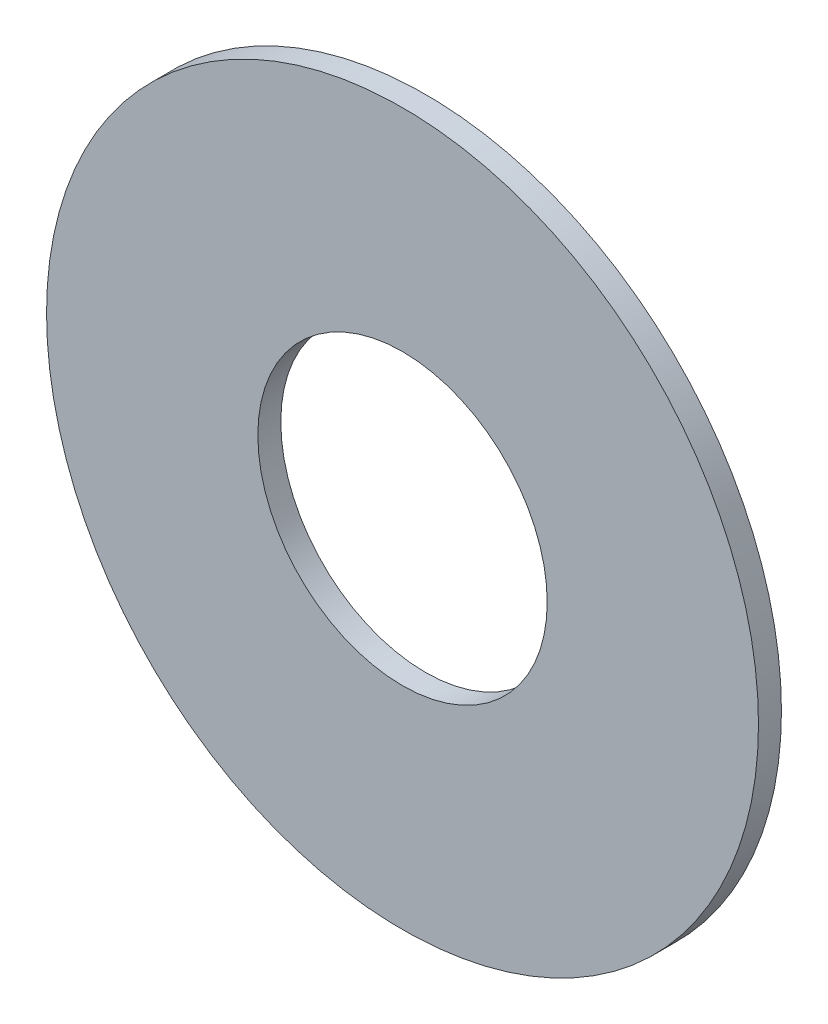
SolidWorks part; units mm, degrees
ref_plane "Front Plane" through (0, 0, 0) normal (0, 0, 1) x (1, 0, 0)
ref_plane "Top Plane" through (0, 0, 0) normal (0, 1, 0) x (1, 0, 0)
ref_plane "Right Plane" through (0, 0, 0) normal (1, 0, 0) x (0, 0, -1)
sketch "Sketch1" plane through (0, 0, 0) normal (0, 0, 1) x (1, 0, 0)
  circle A0 centre (0, 0) radius 1.6002
  circle A1 centre (0, 0) radius 3.937
  dimension "D1" = 3.2004
  dimension "D2" = 7.874
extrude "Boss-Extrude1" add sketch "Sketch1" along normal blind 0.254
